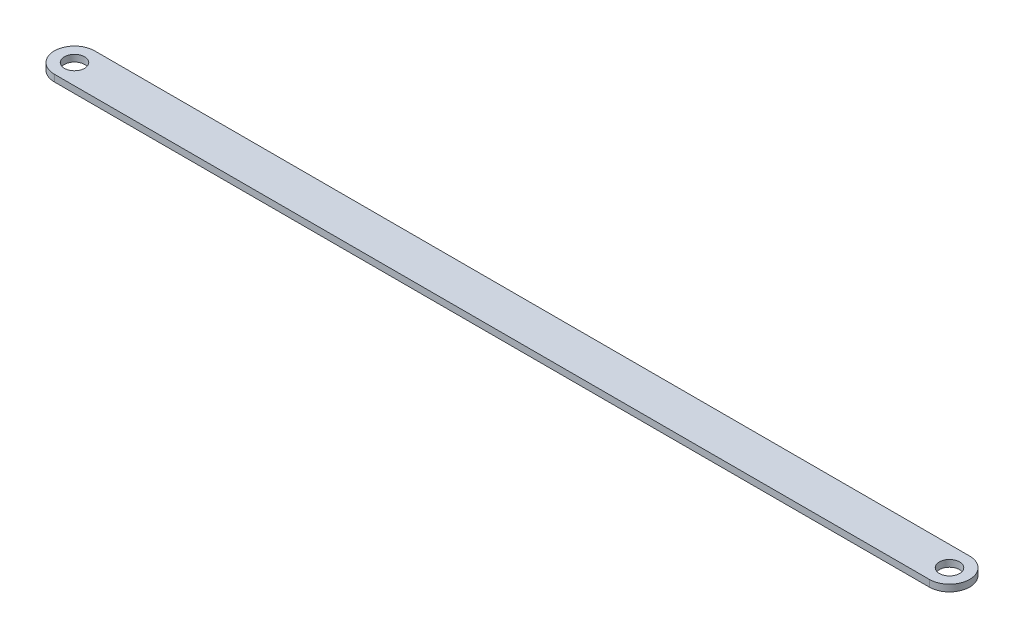
SolidWorks part; units mm, degrees
material "Acrylic (Medium-high impact)"
ref_plane "Front Plane" through (0, 0, 0) normal (0, 0, 1) x (1, 0, 0)
ref_plane "Top Plane" through (0, 0, 0) normal (0, 1, 0) x (1, 0, 0)
ref_plane "Right Plane" through (0, 0, 0) normal (1, 0, 0) x (0, 0, -1)
sketch "Sketch1" plane through (0, 0, 0) normal (0, 1, 0) x (1, 0, 0)
  line L0 (65, 0) -> (-65, 0) construction
  line L1 (65, -3) -> (-65, -3)
  line L2 (65, 3) -> (-65, 3)
  arc A0 (65, -3) -> (65, 3) centre (65, 0) ccw
  arc A1 (-65, 3) -> (-65, -3) centre (-65, 0) ccw
  circle A2 centre (-65, 0) radius 1.5
  circle A3 centre (65, 0) radius 1.5
  point P2 (0, 0)
  dimension "D1" = 130
  dimension "D2" = 3
  dimension "D3" = 3
extrude "Boss-Extrude1" add sketch "Sketch1" along normal blind 1
